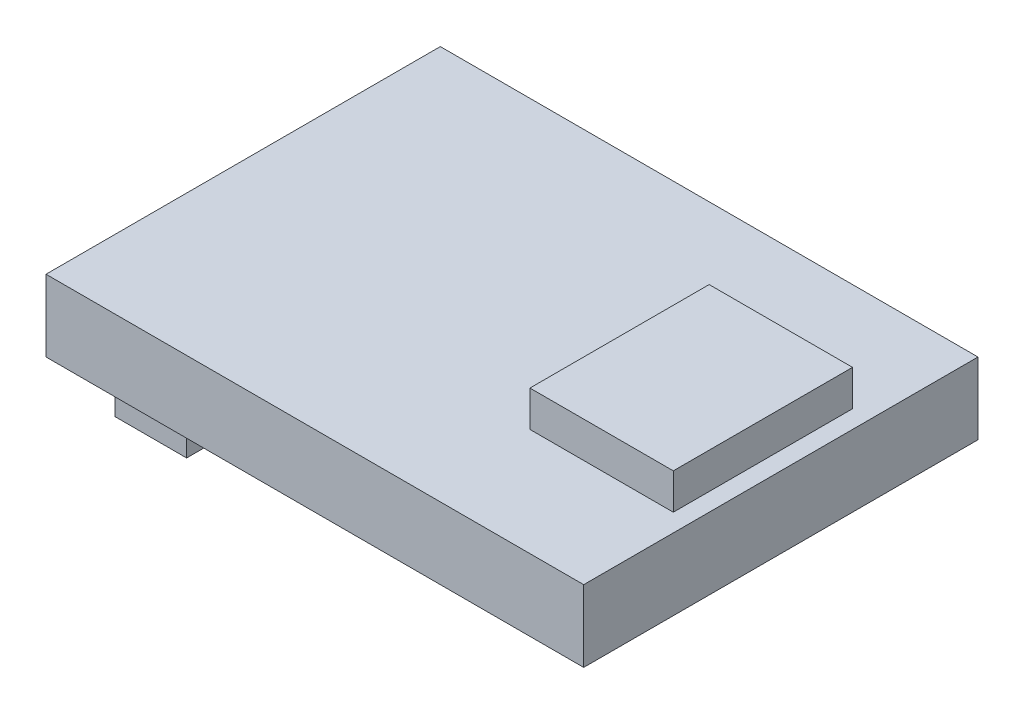
SolidWorks part; units mm, degrees
ref_plane "Front" through (0, 0, 0) normal (0, 0, 1) x (1, 0, 0)
ref_plane "Top" through (0, 0, 0) normal (0, 1, 0) x (1, 0, 0)
ref_plane "Right" through (0, 0, 0) normal (1, 0, 0) x (0, 0, -1)
sketch "스케치1" plane through (0, 0, 0) normal (0, 1, 0) x (1, 0, 0)
  line L1 (-7.5, -5.5) -> (7.5, -5.5)
  line L2 (-7.5, -5.5) -> (-7.5, 5.5)
  line L3 (-7.5, 5.5) -> (7.5, 5.5)
  line L4 (7.5, -5.5) -> (7.5, 5.5)
  line L5 (-7.5, -5.5) -> (7.5, 5.5) construction
  line L6 (-7.5, 5.5) -> (7.5, -5.5) construction
  point P0 (0, 0)
extrude "보스-돌출1" add sketch "스케치1" along normal blind 2
sketch "스케치2" plane through (0, 2, 0) normal (0, 1, 0) x (1, 0, 0)
  line L0 (7.5, -5.5) -> (7.5, 5.5) construction
  line L1 (3, 2.5) -> (7, 2.5)
  line L2 (3, 2.5) -> (3, -2.5)
  line L3 (3, -2.5) -> (7, -2.5)
  line L4 (7, 2.5) -> (7, -2.5)
  line L5 (3, 2.5) -> (7, -2.5) construction
  line L6 (3, -2.5) -> (7, 2.5) construction
  point P0 (5, 0)
  dimension "D1" = 2.5
extrude "보스-돌출2" add sketch "스케치2" along normal blind 1
sketch "스케치3" plane through (0, 0, 0) normal (0, -1, 0) x (1, 0, 0)
  line L1 (-7.0988, -3.9783) -> (-5.0988, -3.9783)
  line L2 (-7.0988, -3.9783) -> (-7.0988, 3.9783)
  line L3 (-7.0988, 3.9783) -> (-5.0988, 3.9783)
  line L4 (-5.0988, -3.9783) -> (-5.0988, 3.9783)
  line L5 (-7.0988, -3.9783) -> (-5.0988, 3.9783) construction
  line L6 (-7.0988, 3.9783) -> (-5.0988, -3.9783) construction
  point P0 (-6.0988, 0)
extrude "보스-돌출3" add sketch "스케치3" along normal blind 2
